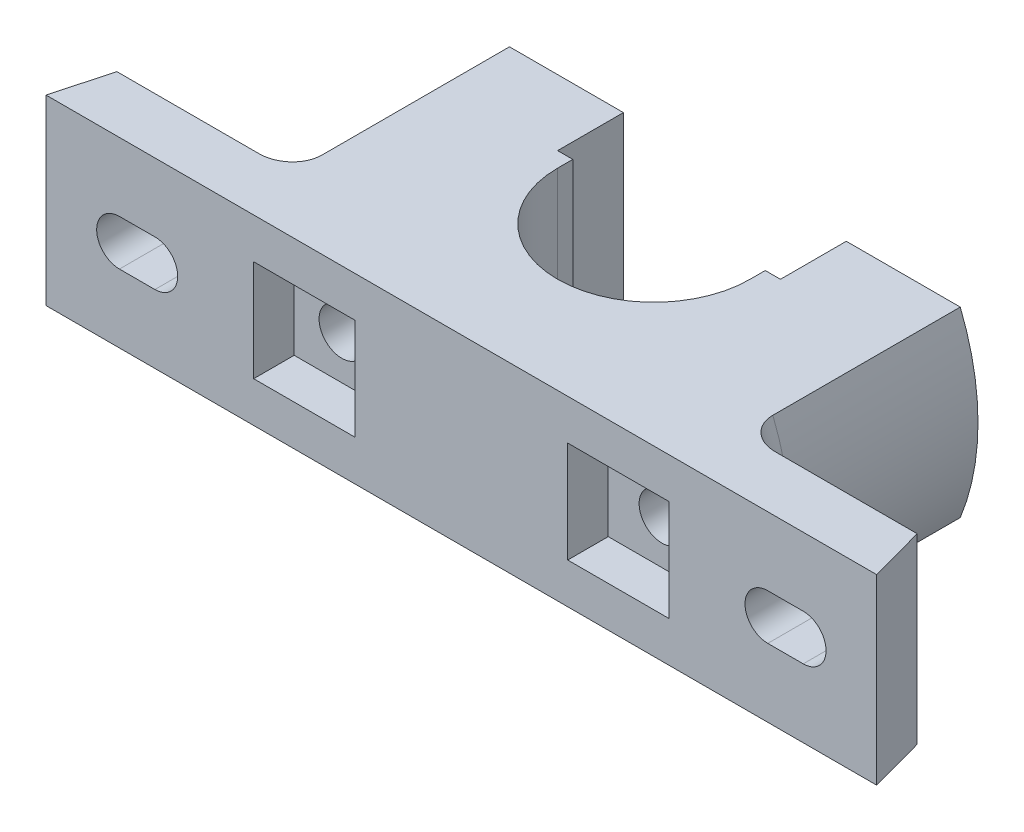
SolidWorks part; units mm, degrees
ref_plane "Front Plane" through (0, 0, 0) normal (0, 0, 1) x (1, 0, 0)
ref_plane "Top Plane" through (0, 0, 0) normal (0, 1, 0) x (1, 0, 0)
ref_plane "Right Plane" through (0, 0, 0) normal (1, 0, 0) x (0, 0, -1)
sketch "Sketch1" plane through (0, 0, 0) normal (0, 1, 0) x (1, 0, 0)
  line L0 (0, 0) -> (0, 85.6146) construction
  line L1 (-82, 0) -> (82, 0)
  line L2 (82, 0) -> (79, 11)
  line L3 (79, 11) -> (50, 11)
  line L4 (50, 11) -> (50, 54)
  line L5 (50, 54) -> (22, 54)
  line L6 (22, 54) -> (22, 41)
  line L7 (22, 41) -> (19, 41)
  line L8 (-22, 41) -> (-19, 41)
  line L9 (-22, 54) -> (-22, 41)
  line L10 (-50, 11) -> (-50, 54)
  line L11 (-79, 11) -> (-50, 11)
  line L12 (-82, 0) -> (-79, 11)
  line L13 (-50, 54) -> (-22, 54)
  line L14 (-19, 41) -> (-19, 38)
  line L15 (19, 41) -> (19, 38)
  arc A0 (-19, 38) -> (19, 38) centre (0, 38) ccw
  dimension "D9" = 13
  dimension "D5" = 50
  dimension "D8" = 16
  dimension "D1" = 164
  dimension "D2" = 3
  dimension "D3" = 54
  dimension "D4" = 11
  dimension "D6" = 44
  dimension "D7" = 38
extrude "Boss-Extrude1" add sketch "Sketch1" along normal mid plane 36
sketch "Sketch2" plane through (0, 0, 0) normal (0, 0, 1) x (1, 0, 0)
  line L1 (-21, -10) -> (-41, -10)
  line L2 (-21, -10) -> (-21, 10)
  line L3 (-21, 10) -> (-41, 10)
  line L4 (-41, -10) -> (-41, 10)
  line L5 (-21, -10) -> (-41, 10) construction
  line L6 (-21, 10) -> (-41, -10) construction
  point P0 (-31, 0)
  dimension "D1" = 20
  dimension "D2" = 20
  dimension "D3" = 31
extrude "Cut-Extrude1" cut sketch "Sketch2" against normal blind 8
hole_wizard "Ø10.0mm Dowel Hole1" positions "Sketch4" profile "Sketch3" hole size "Ø10.0" standard "ANSI Metric"
sketch "Sketch4" plane through (0, 0, -8) normal (0, 0, 1) x (1, 0, 0)
  point P0 (-31.5955, -1.3107)
sketch "Sketch3" plane through (-31.5955, -1.3107, -8) normal (1, 0, 0) x (0, -1, 0)
  line L0 (0, 0) -> (0, 56.7039)
  line L1 (0, 56.7039) -> (4.5, 54)
  line L2 (4.5, 54) -> (4.5, 0)
  line L5 (4.5, 0) -> (0, 0)
  line L10 (0, 56.7039) -> (-4.5, 54) construction
  line L11 (0, -6.35) -> (0, 107.95) construction
  dimension "Hole Dia." = 9
  dimension "Hole Depth" = 54
  dimension "Drill Angle" = 118
sketch "Sketch5" plane through (0, 0, -11) normal (0, 0, -1) x (-1, 0, 0)
  line L0 (60.5, 0) -> (67.5, 0) construction
  line L1 (60.5, 4.5) -> (67.5, 4.5)
  line L2 (60.5, -4.5) -> (67.5, -4.5)
  arc A0 (60.5, 4.5) -> (60.5, -4.5) centre (60.5, 0) ccw
  arc A1 (67.5, -4.5) -> (67.5, 4.5) centre (67.5, 0) ccw
  point P3 (64, 0)
  dimension "D1" = 16
  dimension "D2" = 9
  dimension "D3" = 64
extrude "Cut-Extrude2" cut sketch "Sketch5" against normal blind 11
mirror "Mirror5" about plane through (0, 0, 0) normal (1, 0, 0) of "Cut-Extrude1", "Ø10.0mm Dowel Hole1", "Cut-Extrude2"
hole_wizard "Ø10.0mm Dowel Hole3" positions "3DSketch2" profile "Sketch7" hole size "Ø10.0" standard "ANSI Metric"
sketch3d "3DSketch2"
  point P0 (0, 0, 0)
  point P4 (0, 0, 0)
  point P6 (0, 0, 0)
  point P8 (0, 0, 0)
  point P10 (-0.8545, 0.6808, -19.0192)
sketch "Sketch7" plane through (-0.8545, 0.6808, -19.0192) normal (0, 1, 0) x (-0.999, 0, -0.045)
  line L0 (0, 0) -> (0, 7.8026)
  line L1 (0, 7.8026) -> (3, 6)
  line L2 (3, 6) -> (3, 0)
  line L5 (3, 0) -> (0, 0)
  line L10 (0, 7.8026) -> (-3, 6) construction
  line L11 (0, -6.35) -> (0, 107.95) construction
  dimension "Hole Dia." = 6
  dimension "Hole Depth" = 6
  dimension "Drill Angle" = 118
sketch "Sketch11" plane through (0, 0, -54) normal (0, 0, 1) x (1, 0, 0)
  line L1 (-50, 18) -> (-50, -18) construction
  line L2 (-22, -18) -> (-50, -18) construction
  line L4 (-44.4972, -18) -> (-50, -18)
  line L6 (-50, 18) -> (-50, -18)
  line L8 (-50, 18) -> (-44.4972, 18)
  arc A0 (-44.4972, 18) -> (-44.4972, -18) centre (0, 0) ccw
  dimension "D1" = 96
extrude "Cut-Extrude4" cut sketch "Sketch11" along normal up to surface (43 mm away) contours L4 L6
mirror "Mirror6" about plane through (0, 0, 0) normal (1, 0, 0) of "Cut-Extrude4"
fillet "Fillet1" radius 6 1 edges at (-48, 0, -11)
fillet "Fillet2" radius 6 1 edges at (48, 0, -11)
